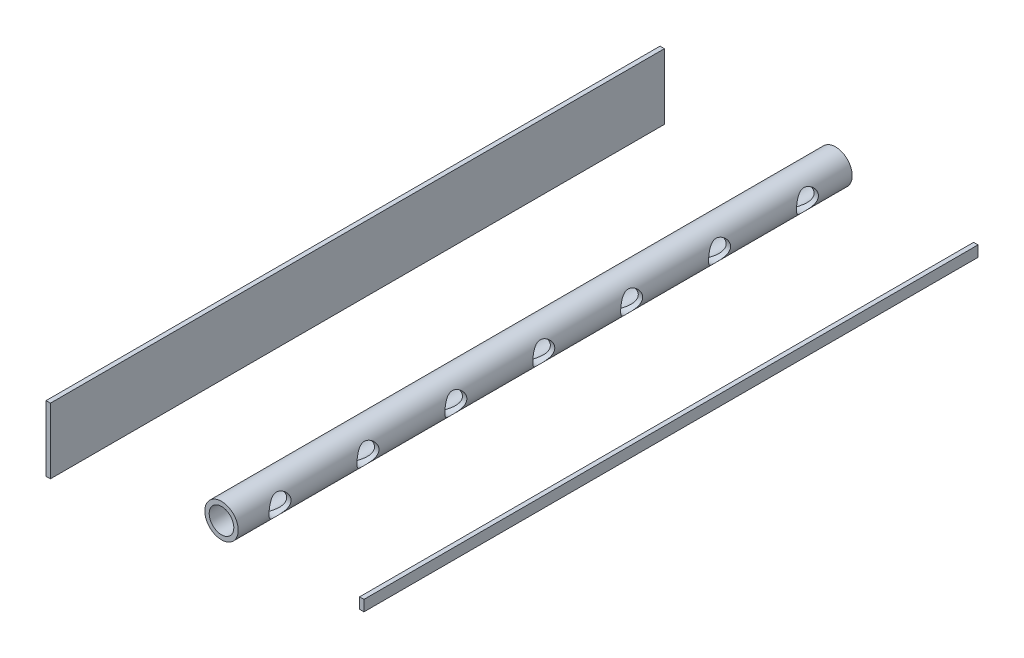
SolidWorks part; units mm, degrees
material "6061-T6 (SS)"
ref_plane "Front Plane" through (0, 0, 0) normal (0, 0, 1) x (1, 0, 0)
ref_plane "Top Plane" through (0, 0, 0) normal (0, 1, 0) x (1, 0, 0)
ref_plane "Right Plane" through (0, 0, 0) normal (1, 0, 0) x (0, 0, -1)
sketch "Sketch1" plane through (0, 0, 0) normal (0, 0, 1) x (1, 0, 0)
  line L0 (-166.3633, -27.8425) -> (138.4367, -27.8425) construction
  line L4 (-106.9108, 8.1599) -> (-104.9118, 8.1599)
  line L5 (-104.9118, 8.1599) -> (-104.9118, -21.6876)
  line L6 (-104.9118, -21.6876) -> (-106.4664, -21.6876)
  line L7 (-106.9108, -21.6876) -> (-106.9108, 8.1599)
  line L17 (35.7765, 2.1818) -> (37.7755, 2.1818)
  line L18 (37.7755, 2.1818) -> (37.7755, -2.7517)
  line L19 (37.7755, -2.7517) -> (35.7765, -2.7517)
  line L20 (35.7765, -2.7517) -> (35.7765, 2.1818)
  line L26 (-106.9108, -21.6876) -> (-106.9108, -21.8128)
  circle A0 centre (-27.0538, 0.8042) radius 5.6
  circle A1 centre (-27.0538, 0.8042) radius 7.6
  spline S0 degree 3 poles (151.4892, -91.8836) (151.4903, -91.8839) (151.4908, -91.884) (151.4909, -91.8836) knots 0.999959 0.999959 0.999959 0.999959 1 1 1 1
  spline S3 degree 3 poles (-106.9108, -21.8128) (-106.7627, -21.7711) (-106.6146, -21.7293) (-106.4664, -21.6876) knots 0.612717 0.612717 0.612717 0.612717 0.613439 0.613439 0.613439 0.613439
  point P9 (-105.9113, -6.239)
  point P14 (-105.9113, 8.1599)
  point P45 (36.776, 2.1818)
  dimension "D4" = 15.2
  dimension "D5" = 11.2
  dimension "D1" = 304.8
  dimension "D2" = 60.452
  dimension "D3" = 1.999
  dimension "D7" = 1.999
extrude "Boss-Extrude1" add sketch "Sketch1" along normal blind 279.4 contours A1 | L20 L19 L18 L17 | L5 L6 S3 L26 L7 L4
ref_plane "Plane1" through (-84.9118, 0, 0) normal (1, 0, 0) x (0, 0, -1)
sketch "Sketch4" plane through (-84.9118, 0, 0) normal (1, 0, 0) x (0, 0, -1)
  circle A0 centre (-260.3507, 0.5103) radius 5
  circle A1 centre (-220.3507, 0.5103) radius 5
  circle A2 centre (-180.3507, 0.5103) radius 5
  circle A3 centre (-140.3507, 0.5103) radius 5
  circle A4 centre (-100.3507, 0.5103) radius 5
  circle A5 centre (-60.3507, 0.5103) radius 5
  circle A6 centre (-20.3507, 0.5103) radius 5
  dimension "D1" = 10
extrude "Cut-Extrude7" cut sketch "Sketch4" along normal blind 76
